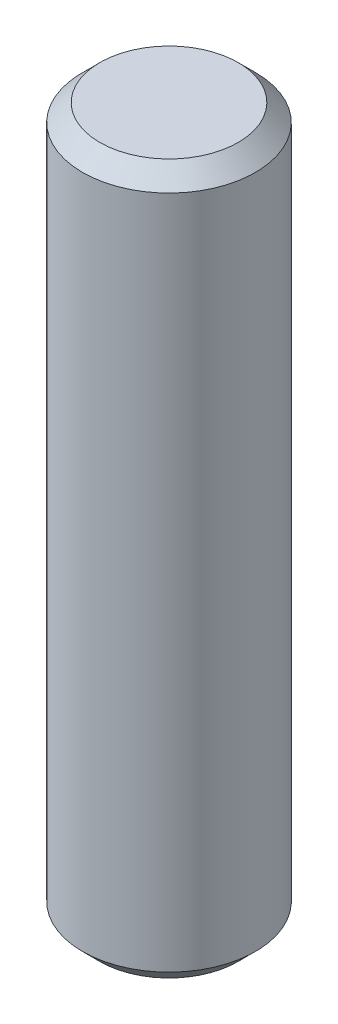
SolidWorks part; units mm, degrees
ref_plane "Спереди" through (0, 0, 0) normal (0, 0, 1) x (1, 0, 0)
ref_plane "Сверху" through (0, 0, 0) normal (0, 1, 0) x (1, 0, 0)
ref_plane "Справа" through (0, 0, 0) normal (1, 0, 0) x (0, 0, -1)
sketch "Эскиз1" plane through (0, 0, 0) normal (0, 0, 1) x (1, 0, 0)
  line L0 (0, 0) -> (0, -12.219) construction
  line L1 (0, 0) -> (0, 41)
  line L2 (0, 41) -> (4, 41)
  line L3 (5, 40) -> (5, 1)
  line L4 (4, 0) -> (0, 0)
  line L5 (5, 1) -> (4, 0)
  line L6 (4, 41) -> (5, 40)
  point P3 (5, 41)
  point P5 (5, 0)
  dimension "D1" = 41
  dimension "D2" = 10
revolve "Повернуть1" add sketch "Эскиз1" angle 360 about L0
